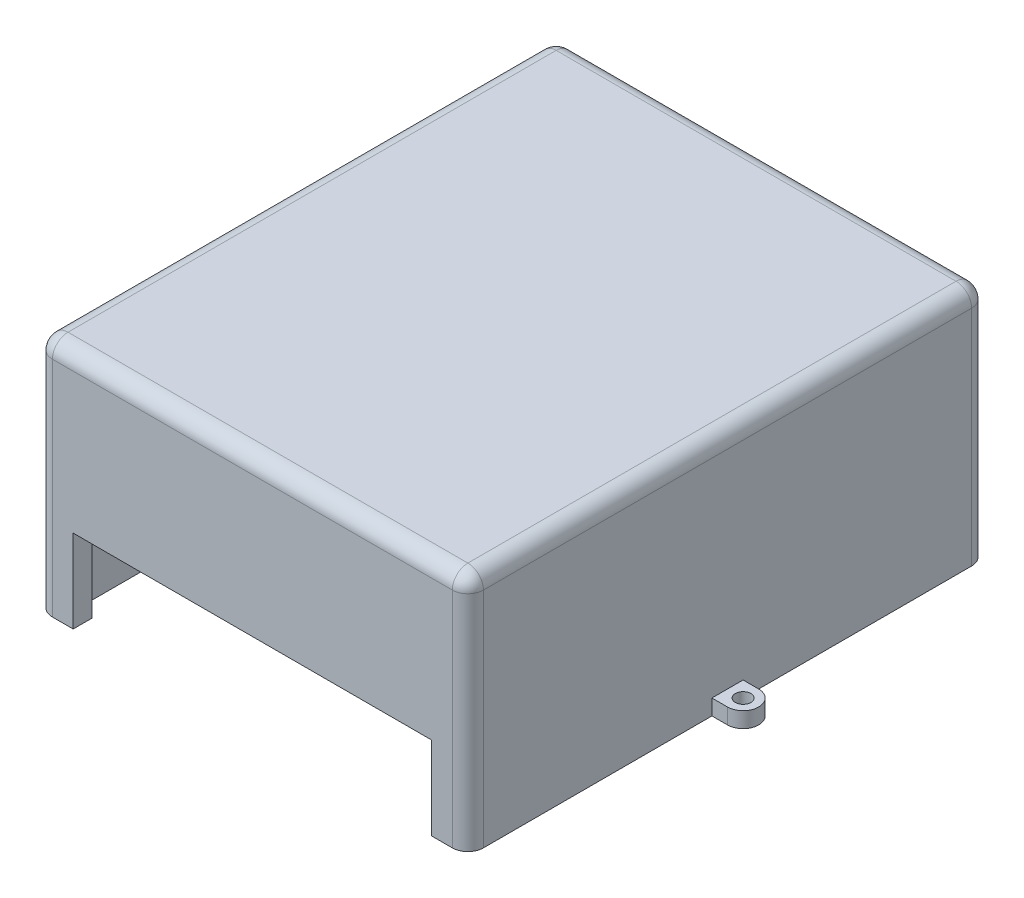
SolidWorks part; units mm, degrees
ref_plane "Alzado" through (0, 0, 0) normal (0, 0, 1) x (1, 0, 0)
ref_plane "Planta" through (0, 0, 0) normal (0, 1, 0) x (1, 0, 0)
ref_plane "Vista lateral" through (0, 0, 0) normal (1, 0, 0) x (0, 0, -1)
sketch "Croquis2" plane through (0, -3.1013, 0) normal (0, 1, 0) x (1, 0, 0)
  line L1 (-55.1603, -222.2506) -> (27.8397, -222.2506)
  line L2 (-55.1603, -222.2506) -> (-55.1603, -122.2506)
  line L3 (-55.1603, -122.2506) -> (27.8397, -122.2506)
  line L4 (27.8397, -222.2506) -> (27.8397, -122.2506)
  line L5 (24.8397, -125.2506) -> (-51.1603, -125.2506)
  line L6 (24.8397, -125.2506) -> (24.8397, -218.5848)
  line L7 (24.8397, -218.5848) -> (-51.1603, -218.5848)
  line L8 (-51.1603, -125.2506) -> (-51.1603, -218.5848)
extrude "Saliente-Extruir1" add sketch "Croquis2" along normal blind 43
sketch "Croquis3" plane through (0, 0, 222.2506) normal (0, 0, 1) x (1, 0, 0)
  line L1 (-55.1603, 39.8987) -> (27.8397, 39.8987)
  line L2 (-55.1603, 39.8987) -> (-55.1603, 42.8987)
  line L3 (-55.1603, 42.8987) -> (27.8397, 42.8987)
  line L4 (27.8397, 39.8987) -> (27.8397, 42.8987)
  dimension "D1" = 3
extrude "Saliente-Extruir2" add sketch "Croquis3" against normal blind 100
sketch "Croquis4" plane through (0, 0, 222.2506) normal (0, 0, 1) x (1, 0, 0)
  line L0 (-55.1603, -3.1013) -> (27.8397, -3.1013) construction
  line L1 (-48.1603, -3.1013) -> (20.8397, -3.1013)
  line L2 (-48.1603, -3.1013) -> (-48.1603, 12.8987)
  line L3 (-48.1603, 12.8987) -> (20.8397, 12.8987)
  line L4 (20.8397, -3.1013) -> (20.8397, 12.8987)
  line L5 (-55.1603, 42.8987) -> (-55.1603, -3.1013) construction
  line L6 (27.8397, 42.8987) -> (27.8397, -3.1013) construction
  dimension "D1" = 7
  dimension "D2" = 7
  dimension "D3" = 16
extrude "Cortar-Extruir3" cut sketch "Croquis4" against normal blind 10
sketch "Croquis5" plane through (0, -3.1013, 0) normal (0, 1, 0) x (1, 0, 0)
  line L0 (-58.1603, -169.2506) -> (-55.1603, -169.2506)
  line L1 (-55.1603, -122.2506) -> (-55.1603, -222.2506) construction
  line L2 (-55.1603, -169.2506) -> (-58.1603, -169.2506) construction
  line L3 (-55.1603, -169.2506) -> (-55.1603, -175.2506)
  line L4 (-55.1603, -175.2506) -> (-58.1603, -175.2506)
  line L5 (-16.6603, -119.2506) -> (-16.6603, -122.2506)
  line L6 (27.8397, -122.2506) -> (-55.1603, -122.2506) construction
  line L7 (-16.6603, -119.2506) -> (-16.6603, -122.2506) construction
  line L8 (-16.6603, -122.2506) -> (-10.6603, -122.2506)
  line L9 (-10.6603, -122.2506) -> (-10.6603, -119.2506)
  line L10 (27.8397, -175.2506) -> (30.8397, -175.2506) construction
  line L11 (30.8397, -169.2506) -> (27.8397, -169.2506) construction
  line L12 (30.8397, -169.2506) -> (27.8397, -169.2506)
  line L13 (27.8397, -122.2506) -> (27.8397, -222.2506) construction
  line L14 (27.8397, -169.2506) -> (27.8397, -175.2506)
  line L15 (27.8397, -175.2506) -> (30.8397, -175.2506)
  arc A0 (-58.1603, -169.2506) -> (-58.1603, -175.2506) centre (-58.1603, -172.2506) ccw
  arc A1 (-58.1603, -169.2506) -> (-58.1603, -175.2506) centre (-58.1603, -172.2506) ccw construction
  arc A2 (-10.6603, -119.2506) -> (-16.6603, -119.2506) centre (-13.6603, -119.2506) ccw
  arc A3 (-10.6603, -119.2506) -> (-16.6603, -119.2506) centre (-13.6603, -119.2506) ccw construction
  arc A4 (30.8397, -175.2506) -> (30.8397, -169.2506) centre (30.8397, -172.2506) ccw
  arc A5 (30.8397, -175.2506) -> (30.8397, -169.2506) centre (30.8397, -172.2506) ccw construction
extrude "Saliente-Extruir3" add sketch "Croquis5" along normal blind 3
sketch "Croquis6" plane through (0, -0.1013, 0) normal (0, 1, 0) x (1, 0, 0)
  circle A0 centre (30.8397, -172.2506) radius 1.5
  circle A1 centre (-13.6603, -119.2506) radius 1.5
  circle A2 centre (-58.1603, -172.2506) radius 1.5
  dimension "D1" = 3
  dimension "D2" = 3
  dimension "D3" = 3
extrude "Cortar-Extruir4" cut sketch "Croquis6" against normal blind 13
fillet "Redondeo1" radius 3 8 edges at (-55.1603, 42.8987, 172.2506) (-13.6603, 42.8987, 222.2506) (-13.6603, 42.8987, 122.2506) (27.8397, 42.8987, 172.2506) (-55.1603, 19.8987, 222.2506) (27.8397, 19.8987, 222.2506) (-55.1603, 19.8987, 122.2506) (27.8397, 19.8987, 122.2506)
fillet "Redondeo2" radius 1 8 edges at (-13.1603, 39.8987, 125.2506) (-51.1603, 39.8987, 171.9177) (-13.1603, 39.8987, 218.5848) (24.8397, 39.8987, 171.9177) (24.8397, 18.3987, 125.2506) (-51.1603, 18.3987, 125.2506) (-51.1603, 18.3987, 218.5848) (24.8397, 18.3987, 218.5848)
